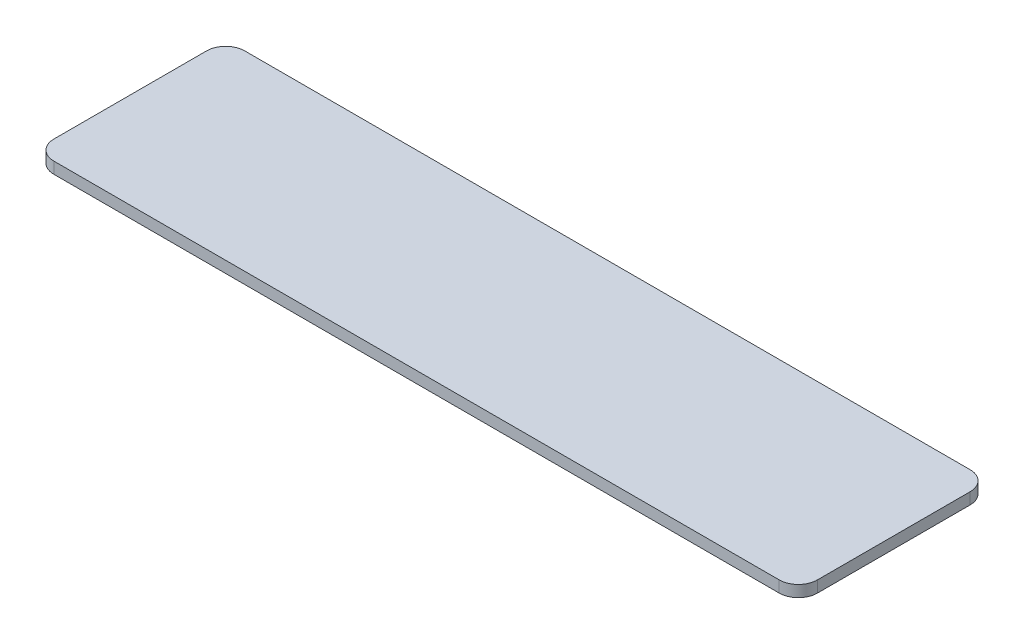
SolidWorks part; units mm, degrees
ref_plane "Front Plane" through (0, 0, 0) normal (0, 0, 1) x (1, 0, 0)
ref_plane "Top Plane" through (0, 0, 0) normal (0, 1, 0) x (1, 0, 0)
ref_plane "Right Plane" through (0, 0, 0) normal (1, 0, 0) x (0, 0, -1)
sketch "Sketch1" plane through (0, 0, 0) normal (0, 1, 0) x (1, 0, 0)
  line L1 (-100, -25) -> (100, -25)
  line L2 (-100, -25) -> (-100, 25)
  line L3 (-100, 25) -> (100, 25)
  line L4 (100, -25) -> (100, 25)
  line L5 (-100, -25) -> (100, 25) construction
  line L6 (-100, 25) -> (100, -25) construction
  point P0 (0, 0)
  dimension "D1" = 200
  dimension "D2" = 50
extrude "Boss-Extrude1" add sketch "Sketch1" along normal blind 3
fillet "Fillet1" radius 5 4 edges at (-100, 1.5, 25) (-100, 1.5, -25) (100, 1.5, -25) (100, 1.5, 25)
